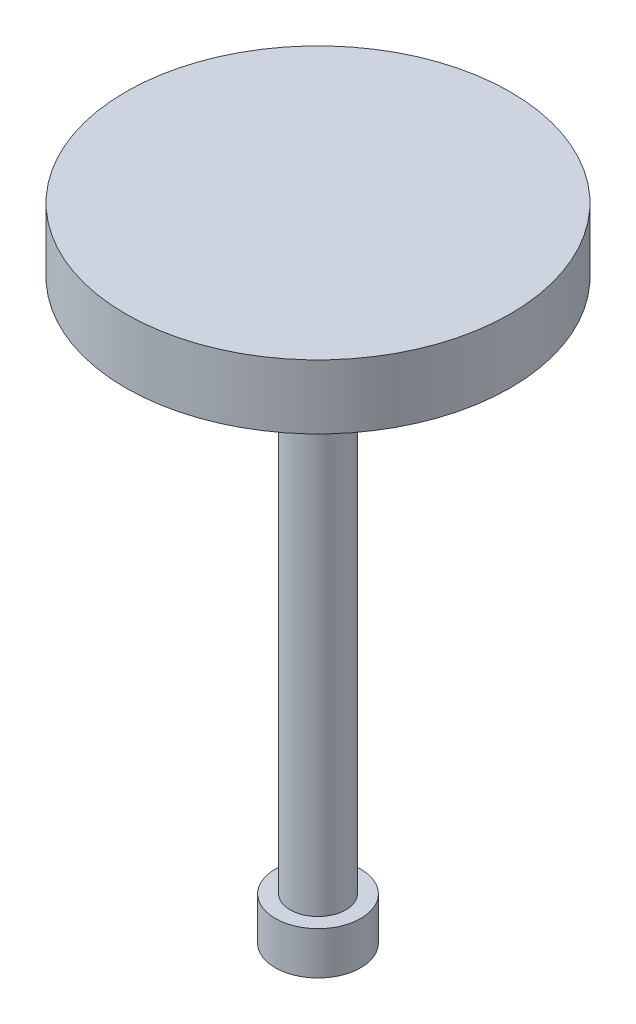
SolidWorks part; units mm, degrees
ref_plane "Front Plane" through (0, 0, 0) normal (0, 0, 1) x (1, 0, 0)
ref_plane "Top Plane" through (0, 0, 0) normal (0, 1, 0) x (1, 0, 0)
ref_plane "Right Plane" through (0, 0, 0) normal (1, 0, 0) x (0, 0, -1)
ref_plane "Plane1" through (0, 0, 0) normal (0, 0, -1) x (-1, 0, 0)
sketch "Sketch1" plane through (0, 0, 0) normal (0, 0, -1) x (-1, 0, 0)
  line L0 (-2, -27) -> (0, -27)
  line L1 (0, -27) -> (0, 3)
  line L2 (0, 3) -> (-9, 3)
  line L3 (-9, 3) -> (-9, 0)
  line L4 (-9, 0) -> (-1.305, 0)
  line L5 (-1.305, 0) -> (-1.305, -25)
  line L6 (-1.305, -25) -> (-2, -25)
  line L7 (-2, -25) -> (-2, -27)
  line L8 (0, -27) -> (0, 3) construction
revolve "Revolve1" add sketch "Sketch1" angle 360 about L8
